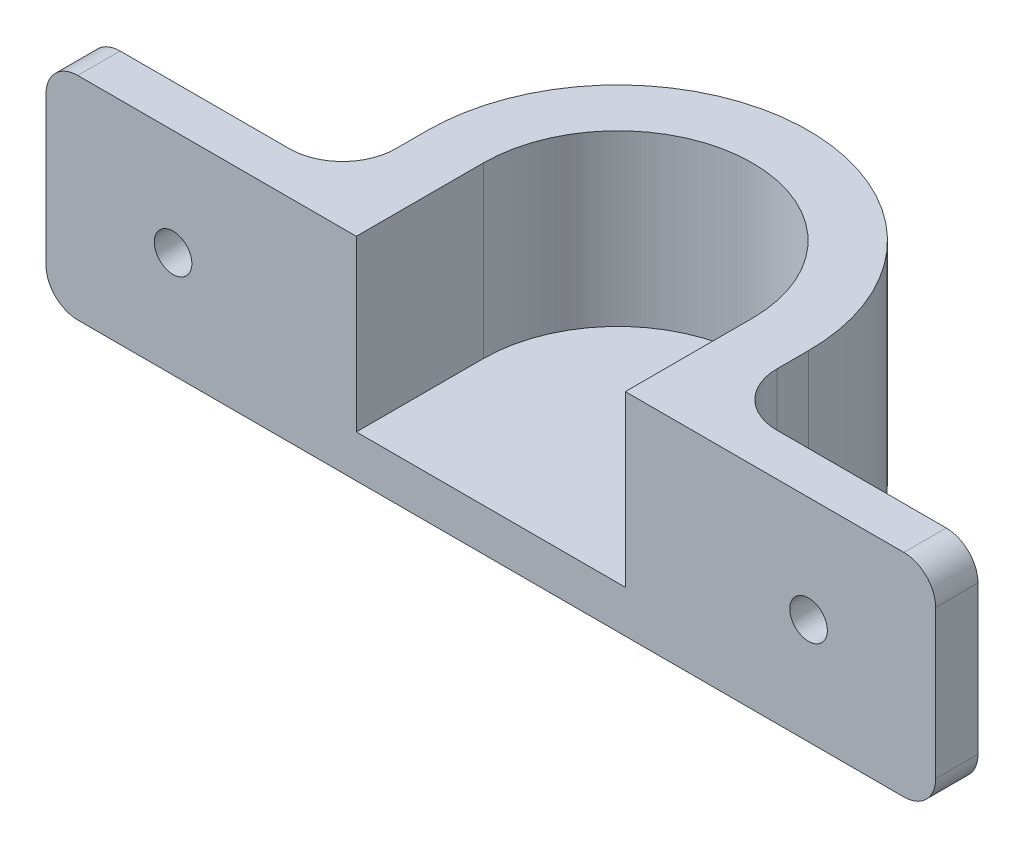
SolidWorks part; units mm, degrees
ref_plane "Front Plane" through (0, 0, 0) normal (0, 0, 1) x (1, 0, 0)
ref_plane "Top Plane" through (0, 0, 0) normal (0, 1, 0) x (1, 0, 0)
ref_plane "Right Plane" through (0, 0, 0) normal (1, 0, 0) x (0, 0, -1)
sketch "Sketch1" plane through (0, 0, 0) normal (0, 1, 0) x (1, 0, 0)
  line L0 (0, 0) -> (0, 4)
  line L1 (0, 4) -> (24, 4)
  line L2 (60, 4) -> (84, 4)
  line L3 (84, 4) -> (84, 0)
  line L6 (29.3, 12) -> (29.3, 0)
  line L7 (29.3, 0) -> (0, 0)
  line L8 (54.7, 12) -> (54.7, 0)
  line L9 (54.7, 0) -> (84, 0)
  line L10 (29.3, 12) -> (54.7, 12) construction
  line L11 (24, 12) -> (24, 4)
  line L12 (60, 12) -> (60, 4)
  line L13 (12, 4) -> (12, 0) construction
  line L14 (72, 4) -> (72, 0) construction
  arc A1 (54.7, 12) -> (29.3, 12) centre (42, 12) ccw
  arc A2 (60, 12) -> (24, 12) centre (42, 12) ccw
  dimension "D3" = 12
  dimension "D4" = 18
  dimension "D1" = 12.7
  dimension "D2" = 4
  dimension "D5" = 60
extrude "Boss-Extrude1" add sketch "Sketch1" along normal blind 20
sketch "Sketch2" plane through (0, 0, -4) normal (0, 0, -1) x (-1, 0, 0)
  line L0 (-42, 20) -> (-42, 0) construction
  line L1 (-24, 20) -> (-60, 20) construction
  line L2 (-60, 0) -> (-24, 0) construction
  line L3 (-72, 10) -> (-42, 10) construction
  line L4 (-42, 10) -> (-12, 10) construction
  circle A1 centre (-72, 10) radius 1.775
  circle A2 centre (-12, 10) radius 1.775
  dimension "D1" = 3.55
  dimension "D2" = 60
extrude "Cut-Extrude1" cut sketch "Sketch2" against normal through all
fillet "Fillet1" radius 3 4 edges at (0, 0, -2) (0, 20, -2) (84, 0, -2) (84, 20, -2)
fillet "Fillet2" radius 5 2 edges at (60, 10, -4) (24, 10, -4)
sketch "Sketch4" plane through (0, 0, 0) normal (0, -1, 0) x (1, 0, 0)
  line L0 (29.3, 0) -> (54.7, 0)
  line L1 (54.7, 0) -> (54.7, -12)
  line L2 (29.3, 0) -> (29.3, -12)
  arc A0 (29.3, -12) -> (54.7, -12) centre (42, -12) ccw
extrude "Boss-Extrude2" add sketch "Sketch4" against normal blind 4
